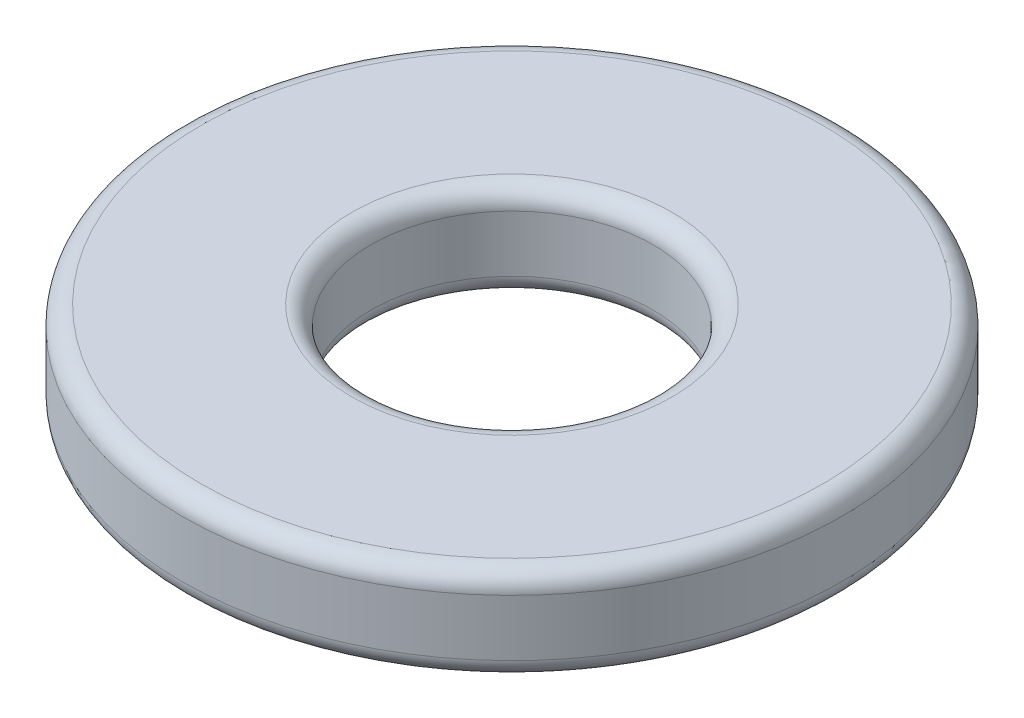
SolidWorks part; units mm, degrees
ref_plane "Ön Düzlem" through (0, 0, 0) normal (0, 0, 1) x (1, 0, 0)
ref_plane "Üst Düzlem" through (0, 0, 0) normal (0, 1, 0) x (1, 0, 0)
ref_plane "Sağ Düzlem" through (0, 0, 0) normal (1, 0, 0) x (0, 0, -1)
sketch "Sketch1" plane through (0, 0, 0) normal (0, 1, 0) x (1, 0, 0)
  circle A0 centre (0, 0) radius 1.5
  circle A1 centre (0, 0) radius 3.5
  dimension "D1" = 3
  dimension "D2" = 7
extrude "Boss-Extrude1" add sketch "Sketch1" along normal blind 1
fillet "Fillet1" radius 0.2 4 edges at (0, 1, 3.5) (0, 0, 1.5) (0, 1, 1.5) (0, 0, 3.5)
